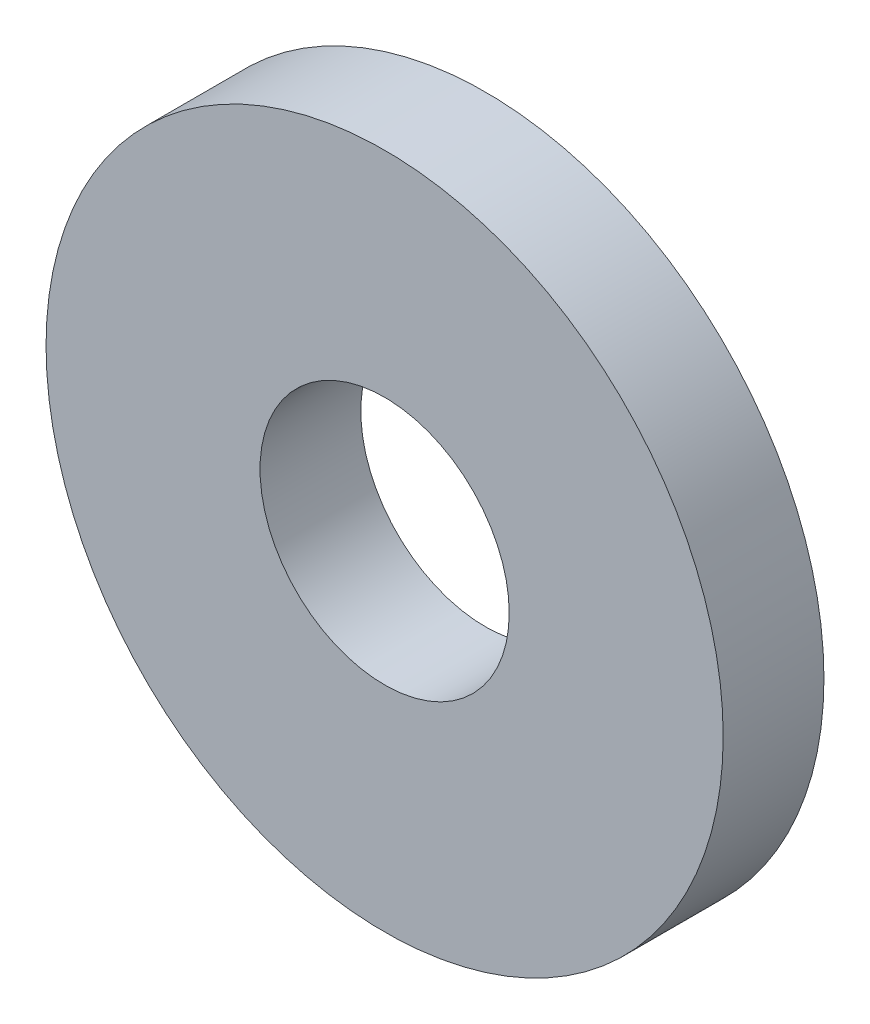
SolidWorks part; units mm, degrees
material "Rubber"
ref_plane "Front Plane" through (0, 0, 0) normal (0, 0, 1) x (1, 0, 0)
ref_plane "Top Plane" through (0, 0, 0) normal (0, 1, 0) x (1, 0, 0)
ref_plane "Right Plane" through (0, 0, 0) normal (1, 0, 0) x (0, 0, -1)
sketch "Sketch1" plane through (0, 0, 0) normal (0, 0, 1) x (1, 0, 0)
  circle A0 centre (0, 0) radius 2.921
  circle A1 centre (0, 0) radius 7.9375
  dimension "ID" = 5.842
  dimension "OD" = 15.875
extrude "Extrude1" add sketch "Sketch1" against normal blind 2.3622
